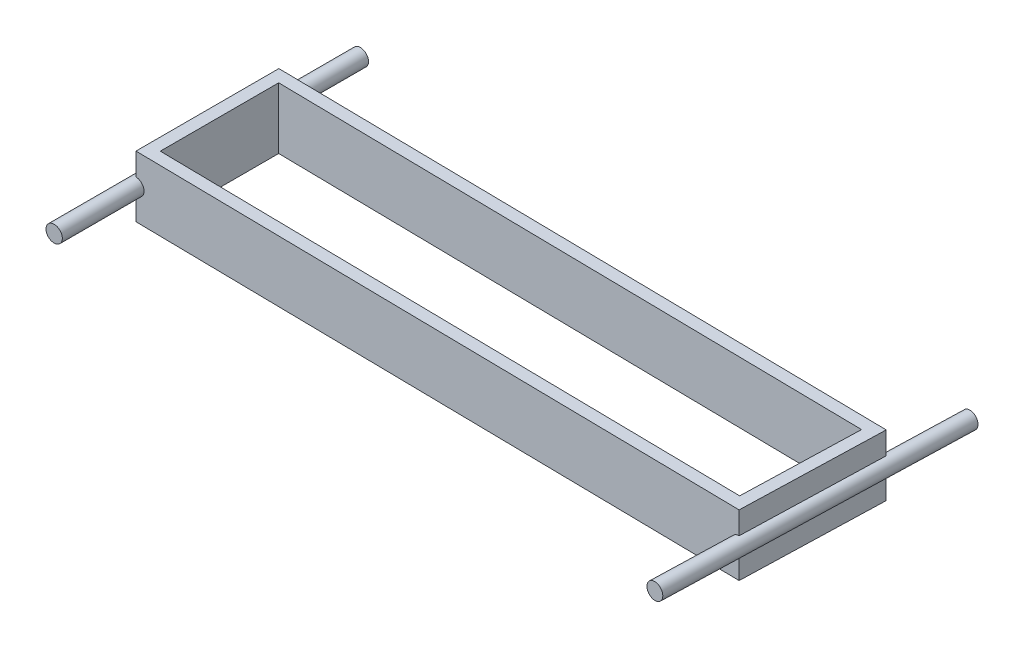
SolidWorks part; units mm, degrees
material "AISI 1020"
ref_plane "Front Plane" through (0, 0, 0) normal (0, 0, 1) x (1, 0, 0)
ref_plane "Top Plane" through (0, 0, 0) normal (0, 1, 0) x (1, 0, 0)
ref_plane "Right Plane" through (0, 0, 0) normal (1, 0, 0) x (0, 0, -1)
sketch "Sketch1" plane through (0, 0, 0) normal (0, 1, 0) x (1, 0, 0)
  line L1 (-323.5787, -44.3357) -> (57.3785, -50.0507)
  line L2 (-323.5787, -44.3357) -> (-323.5787, 44.5643)
  line L3 (-323.5787, 44.5643) -> (60.0452, 38.8093)
  line L4 (57.3785, -50.0507) -> (60.0452, 38.8093)
  line L5 (-315.9587, -36.8291) -> (49.9871, -42.3189)
  line L6 (-315.9587, -36.8291) -> (-315.9587, 36.8291)
  line L7 (-315.9587, 36.8291) -> (52.1966, 31.3062)
  line L8 (49.9871, -42.3189) -> (52.1966, 31.3062)
  line L9 (-1000, 0) -> (49000, 0) construction
  dimension "D1" = 7.62
  dimension "D2" = 7.62
  dimension "D3" = 7.62
  dimension "D4" = 7.62
  dimension "D5" = 88.9
  dimension "D6" = 383.667
  dimension "D7" = 381
extrude "Boss-Extrude1" add sketch "Sketch1" against normal blind 38.1
sketch "Sketch2" plane through (0, 0, 0) normal (0, 0, 1) x (1, 0, 0)
  line L1 (-323.5787, -38.1) -> (-323.5787, 0) construction
  circle A0 centre (-323.5787, -19.05) radius 5.08
  point P4 (-323.5787, -19.05)
  dimension "D1" = 10.16
extrude "Boss-Extrude2" add sketch "Sketch2" along normal mid plane 190.5
ref_plane "Plane2" through (-132.3623, 0, -1.9857) normal (0.9999, 0, 0.015) x (0.015, 0, -0.9999)
mirror "Mirror1" about plane through (-132.3623, 0, -1.9857) normal (0.9999, 0, 0.015) of "Boss-Extrude2"
